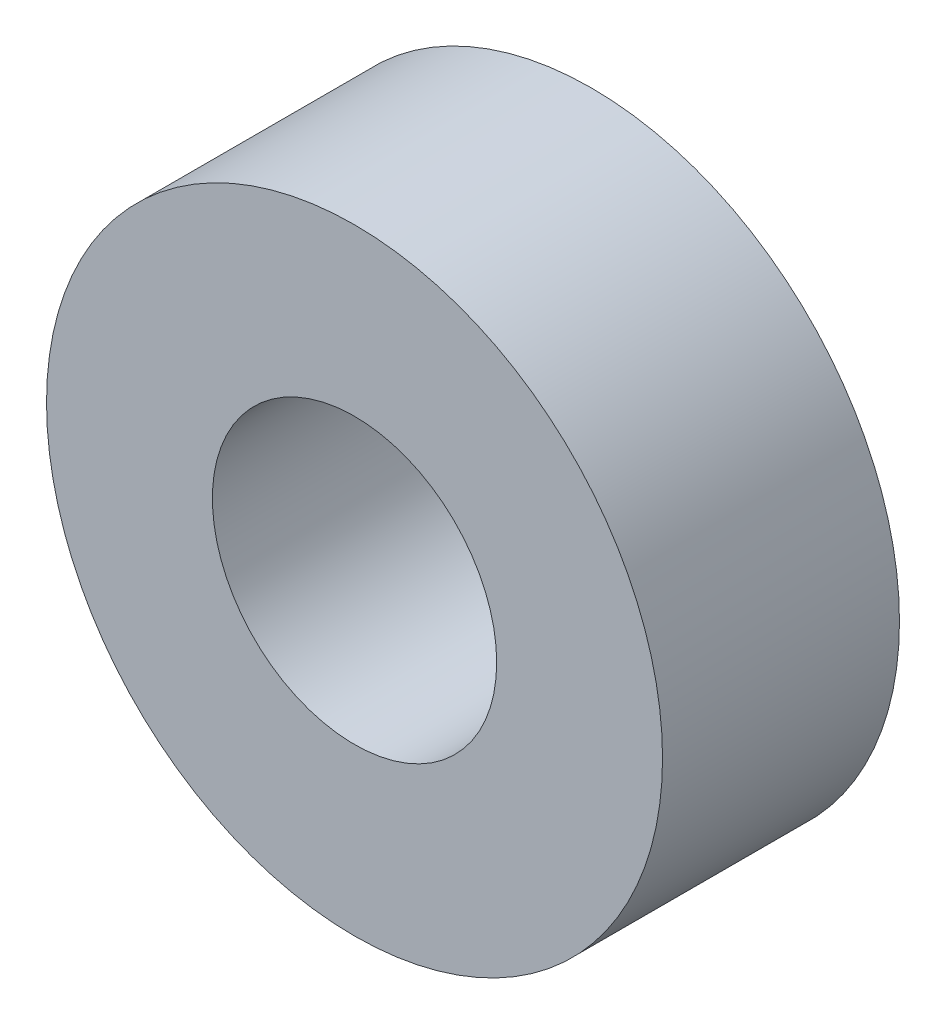
SolidWorks part; units mm, degrees
material "PVC Rigid"
ref_plane "Front Plane" through (0, 0, 0) normal (0, 0, 1) x (1, 0, 0)
ref_plane "Top Plane" through (0, 0, 0) normal (0, 1, 0) x (1, 0, 0)
ref_plane "Right Plane" through (0, 0, 0) normal (1, 0, 0) x (0, 0, -1)
sketch "Sketch1" plane through (0, 0, 0) normal (0, 0, 1) x (1, 0, 0)
  circle A0 centre (0, 0) radius 20.6375
  circle A1 centre (0, 0) radius 9.525
  dimension "D1" = 19.05
  dimension "D2" = 41.275
extrude "Boss-Extrude1" add sketch "Sketch1" along normal blind 15.875
